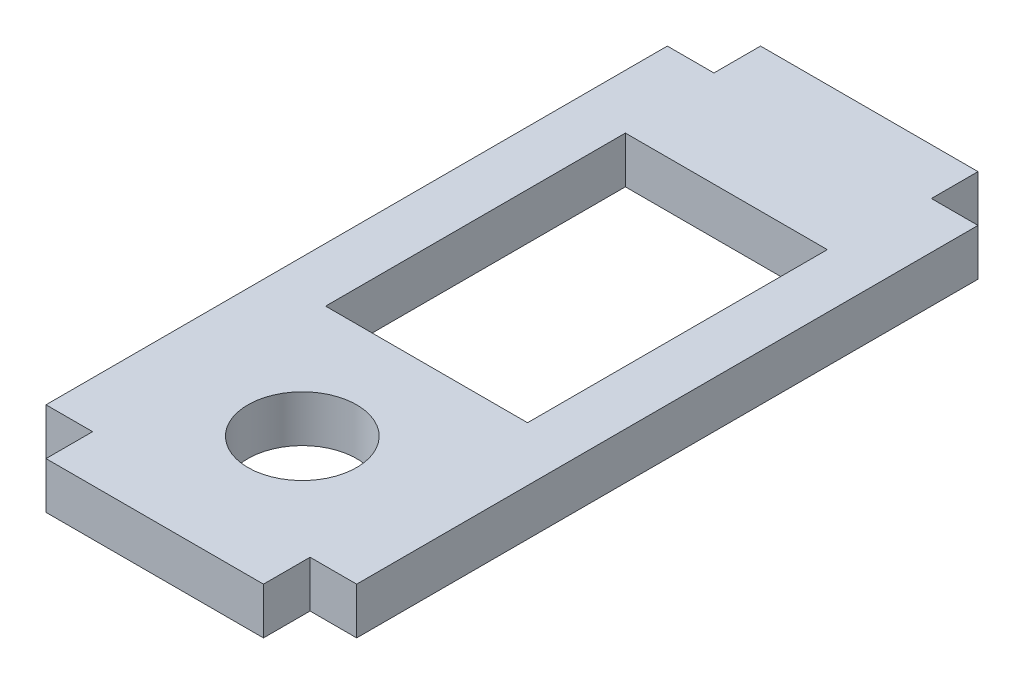
SolidWorks part; units mm, degrees
material "Lasercut ABS"
ref_plane "Front Plane" through (0, 0, 0) normal (0, 0, 1) x (1, 0, 0)
ref_plane "Top Plane" through (0, 0, 0) normal (0, 1, 0) x (1, 0, 0)
ref_plane "Right Plane" through (0, 0, 0) normal (1, 0, 0) x (0, 0, -1)
sketch "Sketch1" plane through (0, 0, 0) normal (0, 1, 0) x (1, 0, 0)
  line L0 (7, 20) -> (10, 20)
  line L1 (-10, 20) -> (-7, 20)
  line L2 (-10, 20) -> (-10, -20)
  line L3 (-10, -20) -> (-7, -20)
  line L4 (10, 20) -> (10, -20)
  line L5 (-7, 23) -> (7, 23)
  line L6 (-7, 23) -> (-7, 20)
  line L7 (-7, -23) -> (7, -23)
  line L8 (7, 23) -> (7, 20)
  line L9 (-7, -20) -> (-7, -23)
  line L10 (7, -20) -> (7, -23)
  line L11 (7, -20) -> (10, -20)
  line L13 (-6.5, 13.8) -> (6.5, 13.8)
  line L14 (-6.5, 13.8) -> (-6.5, -5.5)
  line L15 (-6.5, -5.5) -> (6.5, -5.5)
  line L16 (6.5, 13.8) -> (6.5, -5.5)
  circle A0 centre (0, -13.5) radius 3.5
  point P12 (0, 23)
  point P14 (-10, 0)
  point P21 (0, 13.8)
  dimension "D9" = 7
  dimension "D1" = 40
  dimension "D2" = 20
  dimension "D3" = 14
  dimension "D4" = 3
  dimension "D5" = 13
  dimension "D6" = 19.3
  dimension "D7" = 3
  dimension "D8" = 8
extrude "Boss-Extrude1" add sketch "Sketch1" along normal blind 3
